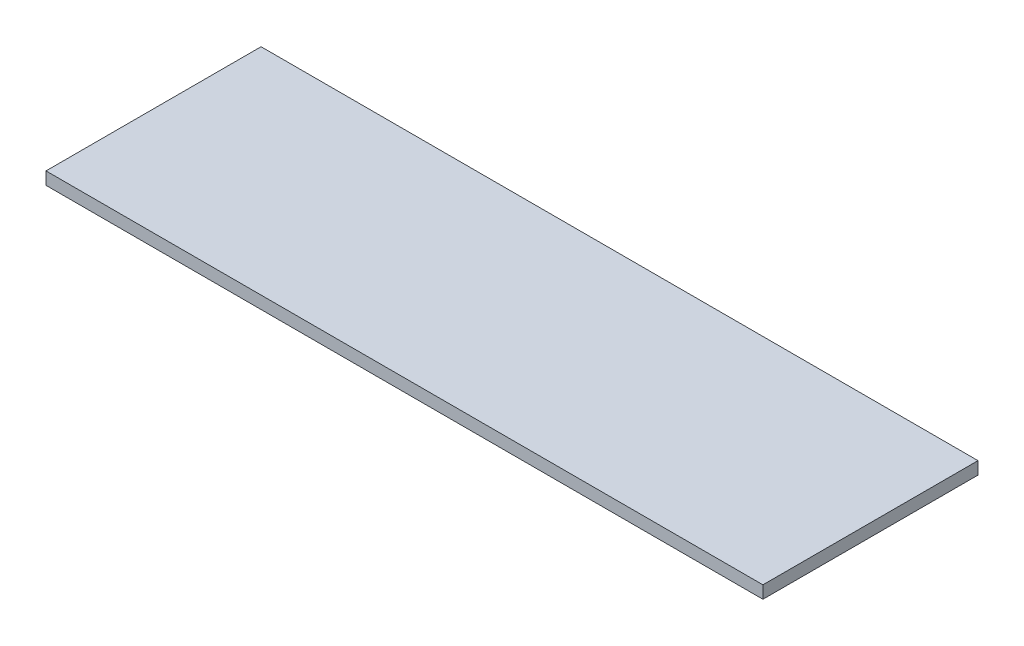
SolidWorks part; units mm, degrees
ref_plane "Front Plane" through (0, 0, 0) normal (0, 0, 1) x (1, 0, 0)
ref_plane "Top Plane" through (0, 0, 0) normal (0, 1, 0) x (1, 0, 0)
ref_plane "Right Plane" through (0, 0, 0) normal (1, 0, 0) x (0, 0, -1)
sketch "Sketch1" plane through (0, 0, 0) normal (0, 1, 0) x (1, 0, 0)
  line L1 (-993.8751, 358.0162) -> (1006.1249, 358.0162)
  line L2 (-993.8751, 358.0162) -> (-993.8751, -241.9838)
  line L3 (-993.8751, -241.9838) -> (1006.1249, -241.9838)
  line L4 (1006.1249, 358.0162) -> (1006.1249, -241.9838)
  line L5 (-993.8751, 358.0162) -> (1006.1249, -241.9838) construction
  line L6 (-993.8751, -241.9838) -> (1006.1249, 358.0162) construction
  point P0 (0, 0)
  dimension "D1" = 2000
  dimension "D2" = 2000
  dimension "D3" = 600
extrude "Boss-Extrude1" add sketch "Sketch1" along normal blind 35
